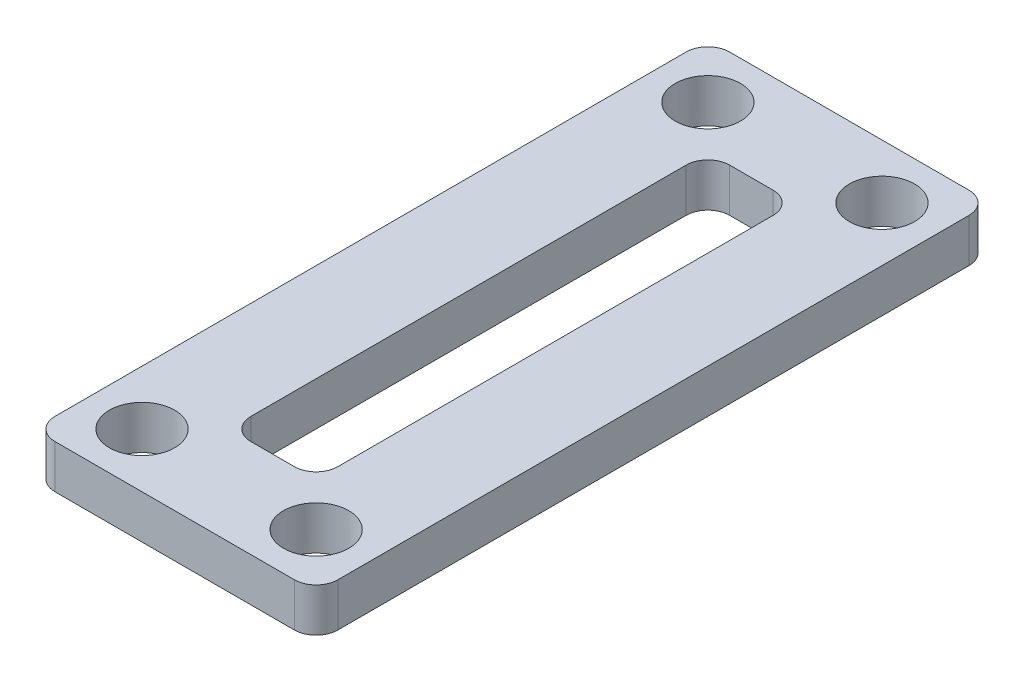
SolidWorks part; units mm, degrees
ref_plane "Front Plane" through (0, 0, 0) normal (0, 0, 1) x (1, 0, 0)
ref_plane "Top Plane" through (0, 0, 0) normal (0, 1, 0) x (1, 0, 0)
ref_plane "Right Plane" through (0, 0, 0) normal (1, 0, 0) x (0, 0, -1)
sketch "Sketch1" plane through (0, 0, 0) normal (0, 1, 0) x (1, 0, 0)
  line L8 (4, -2.5) -> (-2.5, -2.5)
  line L9 (-2.5, -2.5) -> (-2.5, 28.5)
  line L10 (-2.5, 28.5) -> (10.5, 28.5)
  line L11 (10.5, 28.5) -> (10.5, -2.5)
  line L12 (10.5, -2.5) -> (4, -2.5)
  line L17 (4, 2) -> (2, 2)
  line L18 (2, 2) -> (2, 24)
  line L19 (2, 24) -> (6, 24)
  line L20 (6, 24) -> (6, 2)
  line L21 (6, 2) -> (4, 2)
  circle A0 centre (8, 26) radius 1.4
  circle A1 centre (0, 26) radius 1.4
  circle A2 centre (8, 0) radius 1.4
  circle A3 centre (0, 0) radius 1.4
extrude "Boss-Extrude2" add sketch "Sketch1" along normal blind 5.5
fillet "Fillet2" radius 1 8 edges at (6, 2.75, -2) (2, 2.75, -2) (6, 2.75, -24) (2, 2.75, -24) (-2.5, 2.75, -28.5) (10.5, 2.75, -28.5) (-2.5, 2.75, 2.5) (10.5, 2.75, 2.5)
sketch "Sketch2" plane through (0, 5.5, 0) normal (0, 1, 0) x (1, 0, 0)
  circle A0 centre (0, 26) radius 1.5
  circle A1 centre (8, 26) radius 1.5
  circle A2 centre (8, 0) radius 1.5
  circle A3 centre (0, 0) radius 1.5
extrude "Cut-Extrude1" cut sketch "Sketch2" against normal blind 10
sketch "Sketch3" plane through (0, 5.5, 0) normal (0, 1, 0) x (1, 0, 0)
  circle A0 centre (0, 0) radius 36.045
extrude "Cut-Extrude2" cut sketch "Sketch3" against normal blind 0.5
sketch "Sketch4" plane through (0, 5, 0) normal (0, 1, 0) x (1, 0, 0)
  circle A0 centre (0, 0) radius 41.3469
extrude "Cut-Extrude3" cut sketch "Sketch4" against normal blind 1
sketch "Sketch5" plane through (0, 4, 0) normal (0, 1, 0) x (1, 0, 0)
  circle A0 centre (0, 0) radius 64.8741
extrude "Cut-Extrude4" cut sketch "Sketch5" against normal blind 2
